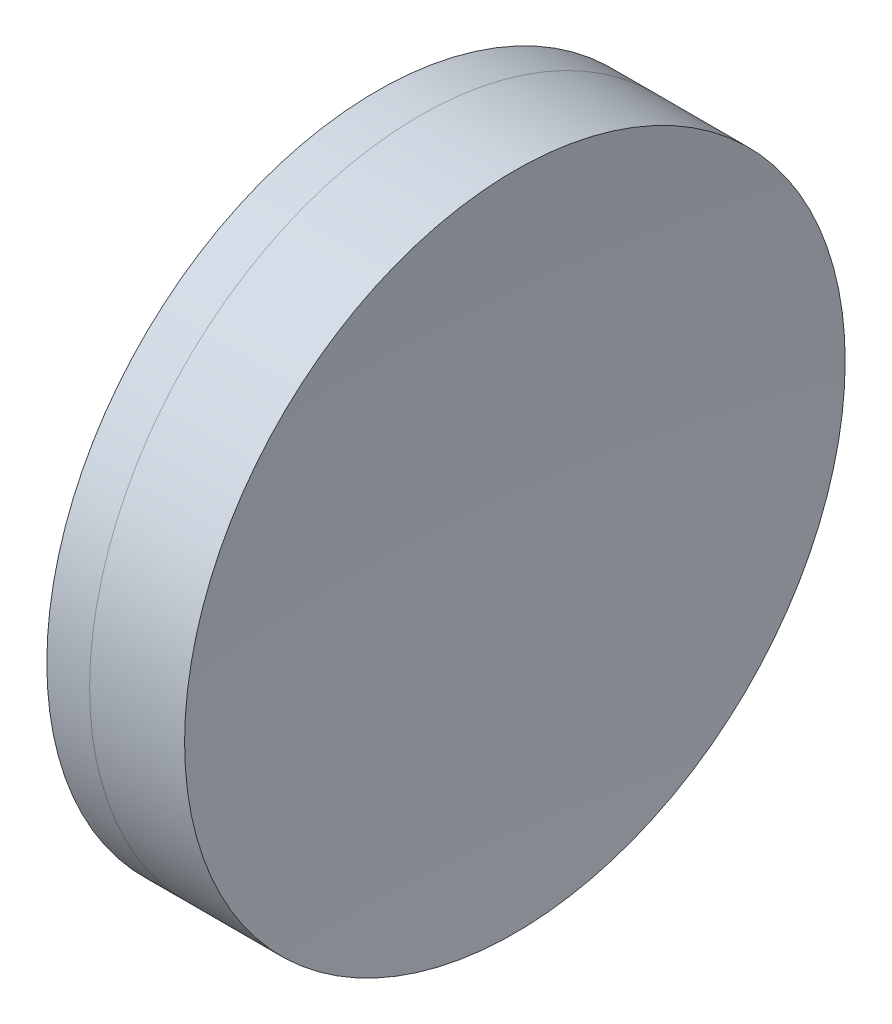
SolidWorks part; units mm, degrees
ref_plane "前视基准面" through (0, 0, 0) normal (0, 0, 1) x (1, 0, 0)
ref_plane "上视基准面" through (0, 0, 0) normal (0, 1, 0) x (1, 0, 0)
ref_plane "右视基准面" through (0, 0, 0) normal (1, 0, 0) x (0, 0, -1)
sketch "草图1" plane through (0, 0, 0) normal (0, 1, 0) x (1, 0, 0)
  line L0 (124.5233, 0) -> (646.9917, 0) construction
  line L1 (337.6466, -12.7) -> (339.2915, -12.7)
  line L2 (337.6466, 12.7) -> (339.2915, 12.7)
  arc A0 (339.2915, -12.7) -> (339.2915, 12.7) centre (262.9405, 0) ccw
  arc A1 (337.6466, 12.7) -> (337.6466, -12.7) centre (398.7405, 0) ccw
  point P10 (336.3405, 0)
  point P11 (340.3405, 0)
  dimension "D3" = 62.4
  dimension "D4" = 77.4
  dimension "D1" = 12.7
  dimension "D2" = 12.7
  dimension "D5" = 4
revolve "旋转1" add sketch "草图1" angle 360 about L0
sketch "草图2" plane through (0, 0, 0) normal (0, 1, 0) x (1, 0, 0)
  line L0 (-0.5519, 0) -> (622.6607, 0) construction
  line L2 (339.2915, 12.7) -> (342.9437, 12.7)
  line L3 (339.2915, -12.7) -> (342.9437, -12.7)
  arc A0 (342.9437, 12.7) -> (342.9437, -12.7) centre (476.3405, 0) ccw
  arc A1 (339.2915, -12.7) -> (339.2915, 12.7) centre (262.9405, 0) ccw construction
  arc A2 (339.2915, -12.7) -> (339.2915, 12.7) centre (262.9405, 0) ccw
  point P4 (340.3405, 0)
  point P8 (342.3405, 0)
  dimension "D1" = 134
  dimension "D2" = 2
revolve "旋转3" add sketch "草图2" angle 360 about L0
